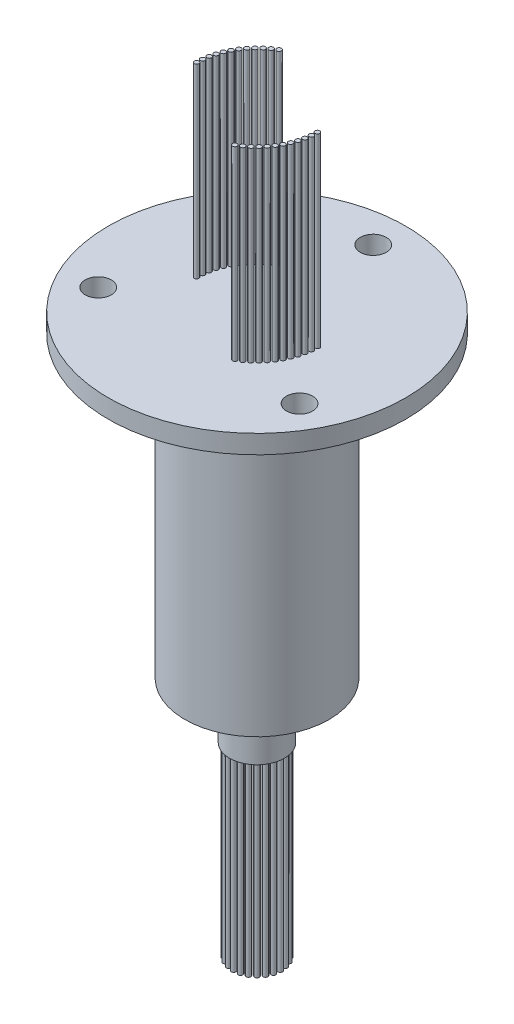
SolidWorks part; units mm, degrees
material "6061-T6 (SS)"
ref_plane "前视基准面" through (0, 0, 0) normal (0, 0, 1) x (1, 0, 0)
ref_plane "上视基准面" through (0, 0, 0) normal (0, 1, 0) x (1, 0, 0)
ref_plane "右视基准面" through (0, 0, 0) normal (1, 0, 0) x (0, 0, -1)
sketch "草图1" plane through (0, 0, 0) normal (0, 0, 1) x (1, 0, 0)
  line L0 (0, 0) -> (0, 40.1) construction
  line L1 (0, 40.1) -> (-16, 40.1)
  line L2 (-16, 40.1) -> (-16, 38.1)
  line L3 (-16, 38.1) -> (-7.75, 38.1)
  line L4 (-7.75, 38.1) -> (-7.75, 6)
  line L5 (-7.75, 6) -> (-2.95, 6)
  line L6 (-2.95, 6) -> (-2.95, 0)
  line L7 (-2.95, 0) -> (0, 0)
  line L8 (0, 0) -> (0, 40.1)
  dimension "D1" = 34.1
  dimension "D2" = 2
  dimension "D3" = 15.5
  dimension "D4" = 5.9
  dimension "D5" = 32
  dimension "D6" = 6
revolve "旋转1" add sketch "草图1" angle 360 about L0
sketch "草图2" plane through (0, 40.1, 0) normal (0, 1, 0) x (1, 0, 0)
  circle A0 centre (0, 0) radius 12.5 construction
  circle A1 centre (0, 12.5) radius 1.4
  circle A2 centre (10.8253, -6.25) radius 1.4
  circle A3 centre (-10.8253, -6.25) radius 1.4
  point P11 (0, 0)
  dimension "D1" = 25
  dimension "D2" = 2.8
  dimension "D3" = 3
extrude "切除-拉伸1" cut sketch "草图2" against normal blind 10
sketch "草图3" plane through (0, 40.1, 0) normal (0, 1, 0) x (1, 0, 0)
  line L0 (0, 0) -> (-6.5, 0) construction
  line L1 (-3.25, 5.6292) -> (0, 0) construction
  circle A0 centre (0, 0) radius 6.5 construction
  circle A1 centre (-6.5, 0) radius 0.25
  circle A2 centre (6.5, 0) radius 0.25
  circle A3 centre (-6.4706, 0.6179) radius 0.25
  circle A4 centre (6.4706, -0.6179) radius 0.25
  circle A5 centre (-6.3825, 1.2301) radius 0.25
  circle A6 centre (6.3825, -1.2301) radius 0.25
  circle A7 centre (-6.2367, 1.8313) radius 0.25
  circle A8 centre (6.2367, -1.8313) radius 0.25
  circle A9 centre (-6.0344, 2.4158) radius 0.25
  circle A10 centre (6.0344, -2.4158) radius 0.25
  circle A11 centre (-5.7774, 2.9785) radius 0.25
  circle A12 centre (5.7774, -2.9785) radius 0.25
  circle A13 centre (-5.4681, 3.5142) radius 0.25
  circle A14 centre (5.4681, -3.5142) radius 0.25
  circle A15 centre (-5.1093, 4.018) radius 0.25
  circle A16 centre (5.1093, -4.018) radius 0.25
  circle A17 centre (-4.7043, 4.4855) radius 0.25
  circle A18 centre (4.7043, -4.4855) radius 0.25
  circle A19 centre (-4.2566, 4.9124) radius 0.25
  circle A20 centre (4.2566, -4.9124) radius 0.25
  circle A21 centre (-3.7704, 5.2947) radius 0.25
  circle A22 centre (3.7704, -5.2947) radius 0.25
  circle A23 centre (-3.25, 5.6292) radius 0.25
  circle A24 centre (3.25, -5.6292) radius 0.25
  dimension "D1" = 13
  dimension "D2" = 0.5
  dimension "D4" = 6.5
  dimension "D5" = 60
  dimension "D3" = 12
extrude "凸台-拉伸1" add sketch "草图3" along normal blind 20
sketch "草图4" plane through (0, 0, 0) normal (0, -1, 0) x (1, 0, 0)
  circle A0 centre (0, 0) radius 2.5 construction
  circle A1 centre (0, -2.5) radius 0.25
  circle A2 centre (-0.647, -2.4148) radius 0.25
  circle A3 centre (-1.25, -2.1651) radius 0.25
  circle A4 centre (-1.7678, -1.7678) radius 0.25
  circle A5 centre (-2.1651, -1.25) radius 0.25
  circle A6 centre (-2.4148, -0.647) radius 0.25
  circle A7 centre (-2.5, 0) radius 0.25
  circle A8 centre (-2.4148, 0.647) radius 0.25
  circle A9 centre (-2.1651, 1.25) radius 0.25
  circle A10 centre (-1.7678, 1.7678) radius 0.25
  circle A11 centre (-1.25, 2.1651) radius 0.25
  circle A12 centre (-0.647, 2.4148) radius 0.25
  circle A13 centre (0, 2.5) radius 0.25
  circle A14 centre (0.647, 2.4148) radius 0.25
  circle A15 centre (1.25, 2.1651) radius 0.25
  circle A16 centre (1.7678, 1.7678) radius 0.25
  circle A17 centre (2.1651, 1.25) radius 0.25
  circle A18 centre (2.4148, 0.647) radius 0.25
  circle A19 centre (2.5, 0) radius 0.25
  circle A20 centre (2.4148, -0.647) radius 0.25
  circle A21 centre (2.1651, -1.25) radius 0.25
  circle A22 centre (1.7678, -1.7678) radius 0.25
  circle A23 centre (1.25, -2.1651) radius 0.25
  circle A24 centre (0.647, -2.4148) radius 0.25
  point P53 (0, 0)
  dimension "D1" = 0.5
  dimension "D2" = 5
  dimension "D3" = 24
extrude "凸台-拉伸2" add sketch "草图4" along normal blind 20
